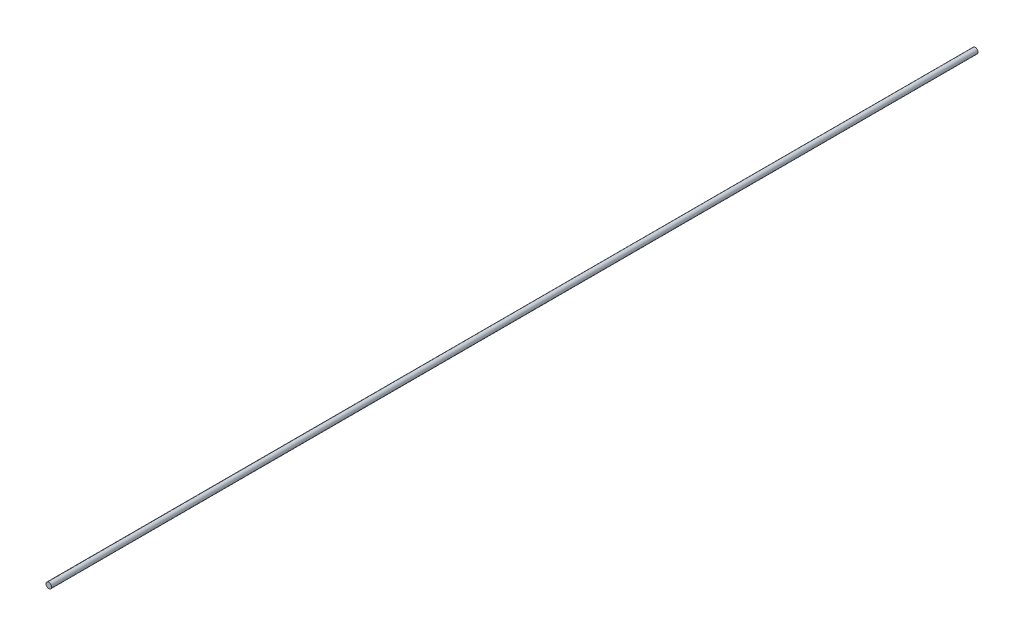
SolidWorks part; units mm, degrees
material "AISI 1020 Steel, Cold Rolled"
ref_plane "Front Plane" through (0, 0, 0) normal (0, 0, 1) x (1, 0, 0)
ref_plane "Top Plane" through (0, 0, 0) normal (0, 1, 0) x (1, 0, 0)
ref_plane "Right Plane" through (0, 0, 0) normal (1, 0, 0) x (0, 0, -1)
sketch "Sketch1" plane through (0, 0, 0) normal (0, 0, 1) x (1, 0, 0)
  circle A0 centre (0, 0) radius 6
  dimension "D1" = 12
extrude "Boss-Extrude1" add sketch "Sketch1" along normal mid plane 2000
cosmetic thread "Cosmetic Thread3" parameters "D2"=6.619
